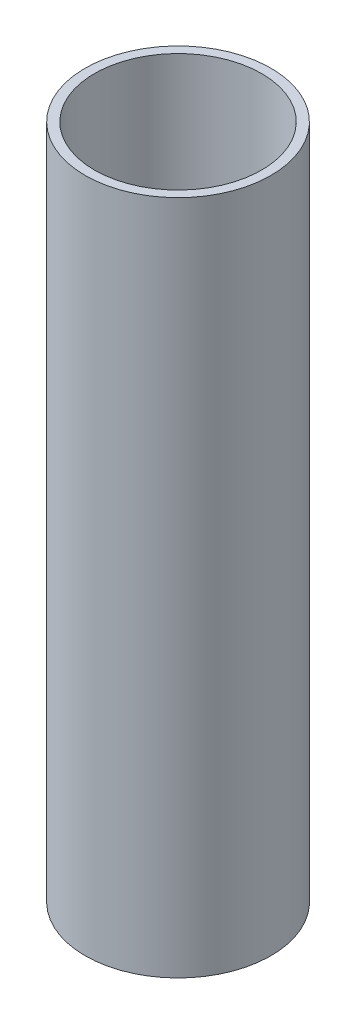
SolidWorks part; units mm, degrees
ref_plane "Front Plane" through (0, 0, 0) normal (0, 0, 1) x (1, 0, 0)
ref_plane "Top Plane" through (0, 0, 0) normal (0, 1, 0) x (1, 0, 0)
ref_plane "Right Plane" through (0, 0, 0) normal (1, 0, 0) x (0, 0, -1)
sketch "Sketch1" plane through (0, 0, 0) normal (0, 1, 0) x (1, 0, 0)
  circle A0 centre (0, 0) radius 16.5
  circle A1 centre (0, 0) radius 14.85
  dimension "D1" = 29.7
  dimension "D2" = 33
extrude "Boss-Extrude1" add sketch "Sketch1" along normal mid plane 120
